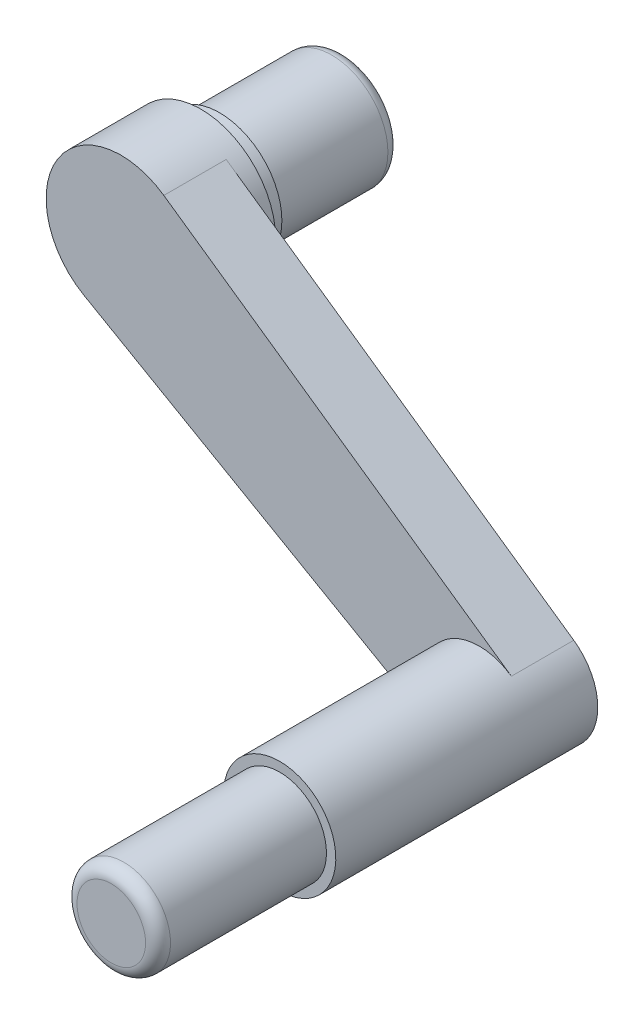
SolidWorks part; units mm, degrees
ref_plane "Ön Düzlem" through (0, 0, 0) normal (0, 0, 1) x (1, 0, 0)
ref_plane "Üst Düzlem" through (0, 0, 0) normal (0, 1, 0) x (1, 0, 0)
ref_plane "Sağ Düzlem" through (0, 0, 0) normal (1, 0, 0) x (0, 0, -1)
sketch "Çizim1" plane through (0, 0, 0) normal (1, 0, 0) x (0, 0, -1)
  line L0 (-55.5808, 0) -> (224.1886, 0) construction
  line L1 (0, 0) -> (0, 60)
  line L2 (0, 60) -> (64, 60)
  line L3 (64, 50) -> (64, 60)
  line L4 (64, 50) -> (79, 50)
  line L5 (79, 50) -> (79, 45)
  line L6 (79, 45) -> (179, 45)
  line L7 (179, 45) -> (179, 0)
  line L8 (0, 0) -> (179, 0)
  dimension "D1" = 60
  dimension "D2" = 64
  dimension "D4" = 15
  dimension "D7" = 100
revolve "Döndür1" add sketch "Çizim1" angle 360 about L0
sketch "Çizim2" plane through (0, 0, 0) normal (0, 0, 1) x (1, 0, 0)
  line L0 (0, 0) -> (249.2271, -158.1118) construction
  line L1 (34.3449, 49.1978) -> (312.9842, -145.32)
  line L2 (-29.8765, -52.0326) -> (264.8181, -221.2428)
  line L3 (34.3449, 49.1978) -> (-29.8765, -52.0326)
  arc A0 (264.8181, -221.2428) -> (312.9842, -145.32) centre (287.2255, -182.2183) ccw
  circle A1 centre (0, 0) radius 60 construction
  dimension "D2" = 90
  dimension "D1" = 340.15
extrude "Yükseklik-Ekstrüzyon2" add sketch "Çizim2" against normal blind 50
sketch "Çizim3" plane through (0, 0, -50) normal (0, 0, -1) x (-1, 0, 0)
  circle A0 centre (-287.2255, -182.2183) radius 45
extrude "Yükseklik-Ekstrüzyon3" add sketch "Çizim3" against normal blind 210
sketch "Çizim4" plane through (0, 0, 160) normal (0, 0, 1) x (1, 0, 0)
  circle A0 centre (287.2255, -182.2183) radius 37.5
  dimension "D1" = 75
extrude "Yükseklik-Ekstrüzyon4" add sketch "Çizim4" along normal blind 135
fillet "Radyus1" radius 10 2 edges at (45, 0, -179) (324.7255, -182.2183, 295)
